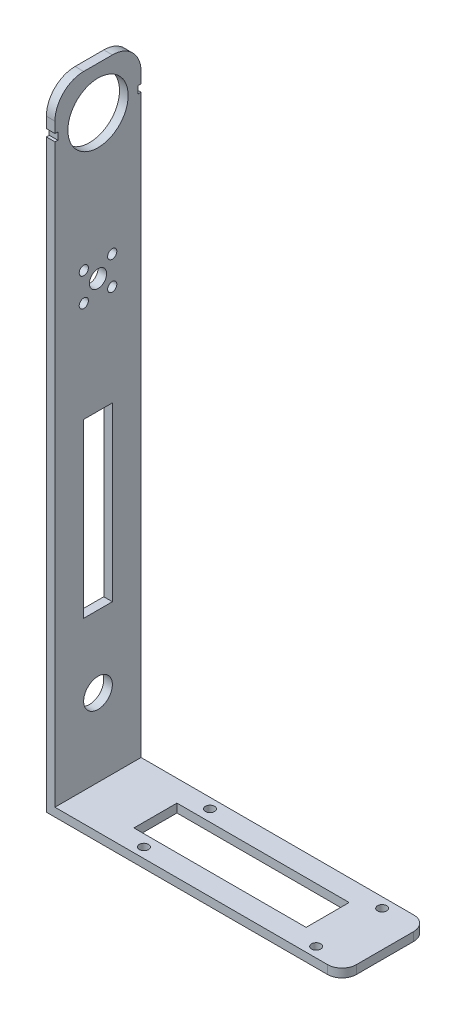
SolidWorks part; units mm, degrees
ref_plane "前视基准面" through (0, 0, 0) normal (0, 0, 1) x (1, 0, 0)
ref_plane "上视基准面" through (0, 0, 0) normal (0, 1, 0) x (1, 0, 0)
ref_plane "右视基准面" through (0, 0, 0) normal (1, 0, 0) x (0, 0, -1)
sketch "草图1" plane through (0, 0, 0) normal (1, 0, 0) x (0, 0, -1)
  line L1 (-15, 85) -> (15, 85)
  line L2 (-15, 85) -> (-15, -85)
  line L3 (-15, -85) -> (15, -85)
  line L4 (15, 85) -> (15, -85)
  line L5 (-15, 85) -> (15, -85) construction
  line L6 (-15, -85) -> (15, 85) construction
  point P0 (0, 0)
  dimension "D1" = 30
  dimension "D2" = 170
extrude "凸台-拉伸1" add sketch "草图1" along normal blind 3
sketch "草图2" plane through (3, 0, 0) normal (1, 0, 0) x (0, 0, -1)
  line L0 (15, -85) -> (15, 85) construction
  line L1 (-15, -85) -> (15, -85)
  line L2 (-15, -85) -> (-15, -82)
  line L3 (-15, -82) -> (15, -82)
  line L4 (15, -85) -> (15, -82)
  dimension "D1" = 3
extrude "凸台-拉伸2" add sketch "草图2" along normal blind 100
sketch "草图4" plane through (0, 0, 0) normal (-1, 0, 0) x (0, 0, 1)
  line L0 (-15, 55) -> (15, 55) construction
  line L1 (-15, -85) -> (-15, 85) construction
  line L2 (15, 85) -> (15, -85) construction
  line L3 (-15, 85) -> (15, 55) construction
  line L4 (15, 85) -> (-15, 55) construction
  circle A0 centre (-4.9497, 74.9497) radius 1.6
  circle A1 centre (4.9497, 74.9497) radius 1.6
  circle A2 centre (4.9497, 65.0503) radius 1.6
  circle A3 centre (-4.9497, 65.0503) radius 1.6
  circle A4 centre (0, 70) radius 3
  point P12 (0, 70)
  point P22 (0, 70)
  dimension "D3" = 6
  dimension "D4" = 3.2
  dimension "D1" = 30
  dimension "D5" = 14
  dimension "D2" = 4
extrude "切除-拉伸1" cut sketch "草图4" against normal through all
sketch "草图5" plane through (0, 85, 0) normal (0, 1, 0) x (1, 0, 0)
  line L0 (0, 15) -> (3, 15)
  line L1 (3, 15) -> (3, -15)
  line L2 (3, -15) -> (0, -15)
  line L3 (0, -15) -> (0, 15)
extrude "凸台-拉伸3" add sketch "草图5" along normal blind 50
sketch "草图6" plane through (0, 0, 0) normal (-1, 0, 0) x (0, 0, 1)
  line L0 (0, 135) -> (0, 112.8725) construction
  line L1 (-15, 135) -> (15, 135) construction
  line L2 (-15, -85) -> (-15, 135) construction
  line L3 (-16, 121.25) -> (-14, 121.25)
  line L4 (-16, 121.25) -> (-16, 118.75)
  line L5 (-16, 118.75) -> (-14, 118.75)
  line L6 (-14, 121.25) -> (-14, 118.75)
  line L7 (-16, 121.25) -> (-14, 118.75) construction
  line L8 (-16, 118.75) -> (-14, 121.25) construction
  line L9 (15, 135) -> (15, -85) construction
  line L10 (14, 121.25) -> (16, 121.25)
  line L11 (14, 121.25) -> (14, 118.75)
  line L12 (14, 118.75) -> (16, 118.75)
  line L13 (16, 121.25) -> (16, 118.75)
  line L14 (14, 121.25) -> (16, 118.75) construction
  line L15 (14, 118.75) -> (16, 121.25) construction
  line L16 (0, 120) -> (15, 120) construction
  line L17 (0, 120) -> (-15, 120) construction
  circle A0 centre (0, 120) radius 10.5
  point P4 (-15, 120)
  point P13 (15, 120)
  dimension "D1" = 21
  dimension "D2" = 15
  dimension "D3" = 2.5
  dimension "D4" = 2.5
  dimension "D5" = 2
  dimension "D6" = 2
extrude "切除-拉伸2" cut sketch "草图6" against normal through all
fillet "圆角1" radius 10 2 edges at (1.5, 135, 15) (1.5, 135, -15)
sketch "草图7" plane through (0, -82, 0) normal (0, 1, 0) x (1, 0, 0)
  line L0 (3, 15) -> (103, -15) construction
  line L1 (103, 15) -> (3, -15) construction
  line L2 (53, 0) -> (53, 30.4883) construction
  line L3 (53, 0) -> (103.1068, 0) construction
  line L4 (30.5, 11.5) -> (90.5, 11.5) construction
  line L5 (23, 7.5) -> (83, 7.5)
  line L6 (23, 7.5) -> (23, -7.5)
  line L7 (23, -7.5) -> (83, -7.5)
  line L8 (83, 7.5) -> (83, -7.5)
  line L9 (23, 7.5) -> (83, -7.5) construction
  line L10 (23, -7.5) -> (83, 7.5) construction
  line L11 (103, 15) -> (103, -15) construction
  circle A4 centre (90.5, 11.5) radius 1.6
  circle A6 centre (30.5, 11.5) radius 1.6
  circle A8 centre (90.5, -11.5) radius 1.6
  circle A9 centre (30.5, -11.5) radius 1.6
  dimension "D1" = 3.2
  dimension "D2" = 3.2
  dimension "D3" = 12.5
  dimension "D4" = 60
  dimension "D5" = 15
  dimension "D6" = 60
  dimension "D7" = 23
extrude "切除-拉伸3" cut sketch "草图7" against normal through all
fillet "圆角2" radius 5 2 edges at (103, -83.5, 15) (103, -83.5, -15)
sketch "草图8" plane through (0, 0, 0) normal (-1, 0, 0) x (0, 0, 1)
  line L1 (-5, -30) -> (5, -30)
  line L2 (-5, -30) -> (-5, 30)
  line L3 (-5, 30) -> (5, 30)
  line L4 (5, -30) -> (5, 30)
  line L5 (-5, -30) -> (5, 30) construction
  line L6 (-5, 30) -> (5, -30) construction
  circle A0 centre (0, -55) radius 5
  point P0 (0, 0)
  dimension "D3" = 10
  dimension "D1" = 10
  dimension "D2" = 60
  dimension "D4" = 25
extrude "切除-拉伸4" cut sketch "草图8" against normal through all
